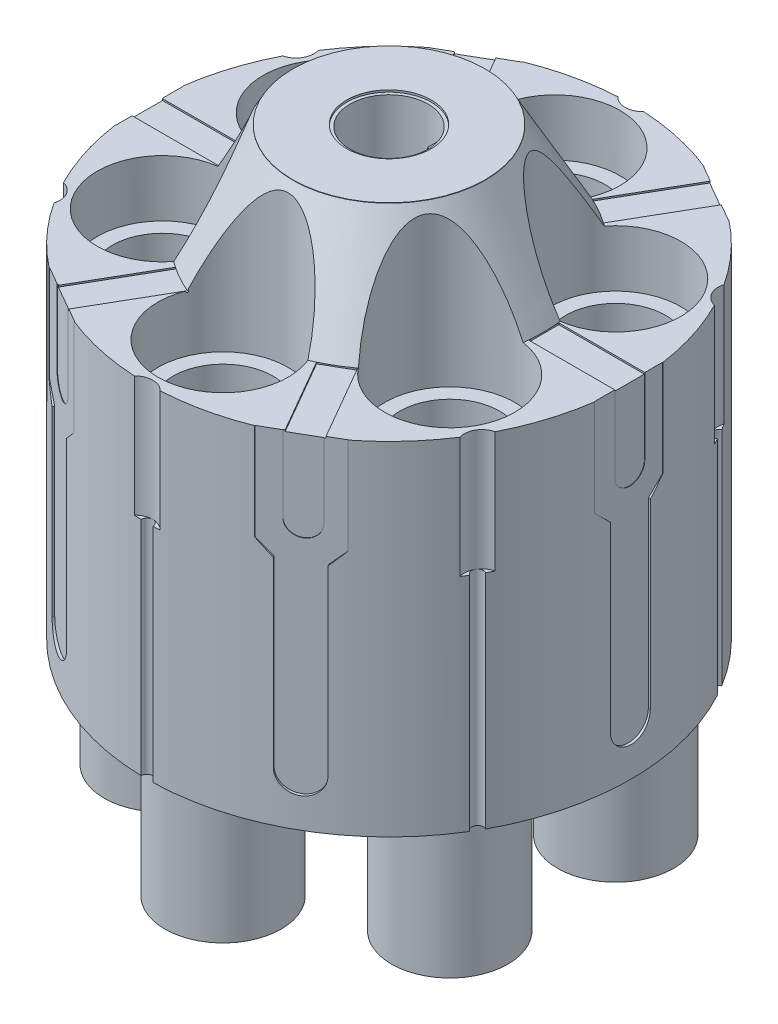
SolidWorks part; units mm, degrees
ref_plane "Front Plane" through (0, 0, 0) normal (0, 0, 1) x (1, 0, 0)
ref_plane "Top Plane" through (0, 0, 0) normal (0, 1, 0) x (1, 0, 0)
ref_plane "Right Plane" through (0, 0, 0) normal (1, 0, 0) x (0, 0, -1)
sketch "Sketch2" plane through (0, 0, 0) normal (0, 1, 0) x (1, 0, 0)
  circle A0 centre (0, 0) radius 30.63
  dimension "D1" = 61.26
extrude "Boss-Extrude2" add sketch "Sketch2" along normal blind 43.34
sketch "Sketch6" plane through (0, 43.34, 0) normal (0, 1, 0) x (1, 0, 0)
  circle A0 centre (0, 0) radius 19.45
  dimension "D1" = 38.9
extrude "Boss-Extrude6" add sketch "Sketch6" along normal blind 13.09
sketch "Sketch8" plane through (0, 0, 0) normal (1, 0, 0) x (0, 0, -1)
  line L0 (0, 56.3789) -> (12.16, 56.3789) construction
  line L1 (0, 31.0365) -> (0, -31.0365) construction
  line L2 (12.16, 56.3789) -> (19.45, 43.34) construction
  line L3 (19.45, 43.34) -> (0, 43.34) construction
  line L4 (30.63, 43.34) -> (-30.63, 43.34) construction
  line L5 (0, 43.34) -> (0, 56.3789) construction
  line L6 (19.45, 43.34) -> (19.45, 56.43)
  line L8 (12.16, 56.3789) -> (19.45, 43.34)
  line L9 (12.16, 56.3789) -> (12.16, 57.4904)
  line L10 (12.16, 57.4904) -> (19.45, 57.4904)
  line L11 (19.45, 57.4904) -> (19.45, 56.43)
  dimension "D1" = 12.16
  dimension "D2" = 13.0389
revolve "Cut-Revolve5" cut sketch "Sketch8" angle 360 about L5
sketch "Sketch9" plane through (0, 56.43, 0) normal (0, 1, 0) x (1, 0, 0)
  line L0 (0, -31.6197) -> (0, 31.6197) construction
  circle A0 centre (0, 20.9948) radius 8.2392
  circle A1 centre (18.182, 10.4974) radius 8.2392
  circle A2 centre (18.182, -10.4974) radius 8.2392
  circle A3 centre (0, -20.9948) radius 8.2392
  circle A4 centre (-18.182, -10.4974) radius 8.2392
  circle A5 centre (-18.182, 10.4974) radius 8.2392
  point P16 (0, 0)
  dimension "D1" = 6
extrude "Cut-Extrude1" cut sketch "Sketch9" against normal blind 20.25
sketch "Sketch10" plane through (0, 36.18, 0) normal (0, 1, 0) x (1, 0, 0)
  line L0 (0, -31.0365) -> (0, 31.0365) construction
  circle A0 centre (0, 20.9948) radius 6.33
  circle A1 centre (0, 20.9948) radius 8.2392 construction
  circle A2 centre (18.182, 10.4974) radius 6.33
  circle A3 centre (18.182, -10.4974) radius 6.33
  circle A4 centre (0, -20.9948) radius 6.33
  circle A5 centre (-18.182, -10.4974) radius 6.33
  circle A6 centre (-18.182, 10.4974) radius 6.33
  point P18 (0, 0)
  dimension "D1" = 12.66
  dimension "D2" = 6
extrude "Cut-Extrude2" cut sketch "Sketch10" against normal through all
sketch "Sketch11" plane through (0, 56.43, 0) normal (0, 1, 0) x (1, 0, 0)
  circle A0 centre (0, 0) radius 4.945
  dimension "D1" = 9.89
extrude "Cut-Extrude3" cut sketch "Sketch11" against normal blind 35.4
sketch "Sketch12" plane through (0, 21.03, 0) normal (0, 1, 0) x (1, 0, 0)
  circle A0 centre (0, 0) radius 2.065
  dimension "D1" = 4.13
extrude "Cut-Extrude4" cut sketch "Sketch12" against normal through all
sketch "Sketch13" plane through (0, 56.43, 0) normal (0, 1, 0) x (1, 0, 0)
  circle A0 centre (0, 0) radius 5.3471
extrude "Cut-Extrude5" cut sketch "Sketch13" against normal blind 0.25
sketch "Sketch15" plane through (0, 21.03, 0) normal (0, 1, 0) x (1, 0, 0)
  line L0 (4.0682, -2.8112) -> (4.0682, -0.81)
  line L1 (4.0682, -0.81) -> (4.8782, -0.81)
  line L2 (4.0682, 2.8112) -> (4.0682, 0.81)
  line L3 (4.0682, 0.81) -> (4.8782, 0.81)
  line L4 (-31.0365, 0) -> (31.0365, 0) construction
  circle A0 centre (0, 0) radius 4.945 construction
  arc A1 (4.0682, -2.8112) -> (4.8782, -0.81) centre (0, 0) ccw
  arc A2 (4.0682, 2.8112) -> (4.8782, 0.81) centre (0, 0) cw
  dimension "D1" = 0.81
  dimension "D2" = 0.81
  dimension "D3" = 0.81
extrude "Boss-Extrude7" add sketch "Sketch15" along normal blind 34.5
sketch "Sketch16" plane through (0, 0, 0) normal (0, -1, 0) x (1, 0, 0)
  circle A0 centre (0, 0) radius 29.6015
  circle A3 centre (-18.182, 10.4974) radius 7.36
  circle A4 centre (0, 20.9948) radius 7.36
  circle A5 centre (18.182, 10.4974) radius 7.36
  circle A6 centre (18.182, -10.4974) radius 7.36
  circle A7 centre (0, -20.9948) radius 7.36
  circle A8 centre (-18.182, -10.4974) radius 7.36
  circle A9 centre (0, 0) radius 4.955
  point P19 (0, 0)
  dimension "D1" = 59.2031
  dimension "D2" = 14.72
  dimension "D4" = 9.91
  dimension "D3" = 6
extrude "Cut-Extrude9" cut sketch "Sketch16" against normal blind 34.5
sketch "Sketch17" plane through (0, 0, 0) normal (0, 1, 0) x (1, 0, 0)
  circle A2 centre (0, 0) radius 4.955
  dimension "D2" = 9.91
extrude "Cut-Extrude12" cut sketch "Sketch17" along normal blind 14.38
sketch "Sketch21" plane through (0, 14.38, 0) normal (0, -1, 0) x (1, 0, 0)
  circle A1 centre (0, 0) radius 3.15
  circle A2 centre (0, 0) radius 4.955
  dimension "D1" = 6.3
extrude "Cut-Extrude14" cut sketch "Sketch21" against normal blind 6.04
sketch "Sketch22" plane through (0, 43.34, 0) normal (0, 1, 0) x (1, 0, 0)
  line L0 (7.9386, 17.6463) -> (16.0129, 31.6314)
  line L1 (11.2272, 15.7476) -> (19.2687, 29.6759)
  line L2 (16.0129, 31.6314) -> (19.2687, 29.6759)
  line L3 (7.9386, 17.6463) -> (11.2272, 15.7476)
  line L4 (19.409, 2.0794) -> (19.409, -1.7179)
  line L5 (19.409, -1.7179) -> (35.492, -1.7179)
  line L6 (35.5576, 2.0794) -> (35.492, -1.7179)
  line L7 (19.409, 2.0794) -> (35.5576, 2.0794)
  line L8 (11.6629, -15.6376) -> (8.3743, -17.5363)
  line L9 (8.3743, -17.5363) -> (16.4158, -31.4646)
  line L10 (19.7372, -29.6227) -> (16.4158, -31.4646)
  line L11 (11.6629, -15.6376) -> (19.7372, -29.6227)
  line L12 (-7.5536, -17.7878) -> (-10.8422, -15.8891)
  line L13 (-10.8422, -15.8891) -> (-18.8837, -29.8174)
  line L14 (-15.6279, -31.7729) -> (-18.8837, -29.8174)
  line L15 (-7.5536, -17.7878) -> (-15.6279, -31.7729)
  line L16 (-19.0239, -2.221) -> (-19.0239, 1.5764)
  line L17 (-19.0239, 1.5764) -> (-35.1069, 1.5764)
  line L18 (-35.1725, -2.221) -> (-35.1069, 1.5764)
  line L19 (-19.0239, -2.221) -> (-35.1725, -2.221)
  line L20 (-11.2778, 15.4961) -> (-7.9892, 17.3947)
  line L21 (-7.9892, 17.3947) -> (-16.0307, 31.3231)
  line L22 (-19.3521, 29.4812) -> (-16.0307, 31.3231)
  line L23 (-11.2778, 15.4961) -> (-19.3521, 29.4812)
  line L25 (-31.0365, 0) -> (31.0365, 0) construction
  point P29 (0.1925, -0.0708)
  dimension "D1" = 6
extrude "Cut-Extrude15" cut sketch "Sketch22" against normal blind 0.2
sketch "Sketch24" plane through (0, 43.34, 0) normal (0, 1, 0) x (1, 0, 0)
  line L0 (30.23, 2.0794) -> (30.23, -1.7179)
  line L1 (30.5593, 2.0794) -> (19.409, 2.0794) construction
  line L2 (19.409, -1.7179) -> (30.5818, -1.7179) construction
  line L3 (30.23, -1.7179) -> (31.9275, -1.7179)
  line L4 (31.9275, -1.7179) -> (31.9275, 2.0794)
  line L5 (31.9275, 2.0794) -> (30.23, 2.0794)
  line L6 (30.63, 0) -> (30.63, 6.5924) construction
  line L7 (-31.0365, 0) -> (31.0365, 0) construction
  line L8 (17.7646, -26.6103) -> (16.9159, -25.1402)
  line L9 (16.9159, -25.1402) -> (13.6272, -27.0389)
  line L10 (13.6272, -27.0389) -> (14.476, -28.509)
  line L11 (14.476, -28.509) -> (17.7646, -26.6103)
  line L12 (-14.1629, -28.6897) -> (-13.3141, -27.2197)
  line L13 (-13.3141, -27.2197) -> (-16.6028, -25.321)
  line L14 (-16.6028, -25.321) -> (-17.4515, -26.791)
  line L15 (-17.4515, -26.791) -> (-14.1629, -28.6897)
  line L16 (-31.9275, -2.0794) -> (-30.23, -2.0794)
  line L17 (-30.23, -2.0794) -> (-30.23, 1.7179)
  line L18 (-30.23, 1.7179) -> (-31.9275, 1.7179)
  line L19 (-31.9275, 1.7179) -> (-31.9275, -2.0794)
  line L20 (-17.7646, 26.6103) -> (-16.9159, 25.1402)
  line L21 (-16.9159, 25.1402) -> (-13.6272, 27.0389)
  line L22 (-13.6272, 27.0389) -> (-14.476, 28.509)
  line L23 (-14.476, 28.509) -> (-17.7646, 26.6103)
  line L24 (14.1629, 28.6897) -> (13.3141, 27.2197)
  line L25 (13.3141, 27.2197) -> (16.6028, 25.321)
  line L26 (16.6028, 25.321) -> (17.4515, 26.791)
  line L27 (17.4515, 26.791) -> (14.1629, 28.6897)
  arc A0 (30.5593, 2.0794) -> (16.8886, 25.5533) centre (0, 0) ccw construction
  point P37 (0, 0)
  dimension "D1" = 0.4
  dimension "D2" = 6
extrude "Cut-Extrude17" cut sketch "Sketch24" against normal blind 9.6
ref_plane "Plane2" through (30.63, 0, 0) normal (1, 0, 0) x (0, 0, -1)
sketch "Sketch26" plane through (30.63, 0, 0) normal (1, 0, 0) x (0, 0, -1)
  line L0 (2.0794, 33.74) -> (-1.7179, 33.74) construction
  line L1 (2.0794, 33.74) -> (-1.7179, 33.74) construction
  line L2 (-1.7179, 33.74) -> (2.0794, 33.74)
  arc A0 (-1.7179, 33.74) -> (2.0794, 33.74) centre (0.1808, 33.74) ccw
extrude "Cut-Extrude18" cut sketch "Sketch26" against normal blind 0.4
pattern_circular "CirPattern1" count 6 over 360 about axis through (0, 43.34, 0) along (0, 1, 0) of "Cut-Extrude18"
sketch "Sketch28" plane through (30.63, 0, 0) normal (1, 0, 0) x (0, 0, -1)
  line L0 (-4.315, 44.0536) -> (4.315, 44.0536)
  line L3 (0, 31.0365) -> (0, -31.0365) construction
  line L4 (-4.315, 44.0536) -> (-4.315, 31.1427)
  line L5 (-4.315, 31.1427) -> (-2.5286, 29.3563)
  line L6 (-2.5286, 29.3563) -> (-2.5286, 6.3189)
  line L7 (4.315, 44.0536) -> (4.315, 31.1427)
  line L8 (4.315, 31.1427) -> (2.5286, 29.3563)
  line L9 (2.5286, 29.3563) -> (2.5286, 6.3189)
  arc A0 (-2.5286, 6.3189) -> (2.5286, 6.3189) centre (0, 6.3189) ccw
  dimension "D1" = 4.315
  dimension "D2" = 4.315
extrude "Cut-Extrude19" cut sketch "Sketch28" against normal blind 0.35
pattern_circular "CirPattern2" count 6 over 360 about axis through (0, 0, 0) along (0, 1, 0) of "Cut-Extrude19"
sketch "Sketch29" plane through (0, 43.34, 0) normal (0, 1, 0) x (1, 0, 0)
  line L0 (-0.7499, 30.6208) -> (-0.7499, 31.6611)
  line L1 (-0.7499, 31.6611) -> (0.7499, 31.6611)
  line L2 (0.7499, 31.6611) -> (0.7499, 30.6208)
  arc A1 (11.4254, 28.4193) -> (-11.4254, 28.4193) centre (0, 0) ccw construction
  arc A2 (-0.7499, 30.6208) -> (0.7499, 30.6208) centre (0, 30.63) ccw
  dimension "D1" = 0.75
extrude "Cut-Extrude23" cut sketch "Sketch29" against normal through all
sketch "Sketch30" plane through (0, 0, 0) normal (0, 1, 0) x (1, 0, 0)
  line L0 (0, -31.0365) -> (0, 31.0365) construction
  line L1 (-1.6376, 30.5862) -> (-1.6376, 31.7494)
  line L2 (-1.6376, 31.7494) -> (1.6376, 31.7494)
  line L3 (1.6376, 31.7494) -> (1.6376, 30.5862)
  arc A0 (-1.6376, 30.5862) -> (1.6376, 30.5862) centre (0, 32.1317) ccw
  arc A1 (-0.7499, 30.6208) -> (-11.4254, 28.4193) centre (0, 0) ccw construction
  arc A2 (11.4254, 28.4193) -> (0.7499, 30.6208) centre (0, 0) ccw construction
  arc A3 (-0.7499, 30.6208) -> (0.7499, 30.6208) centre (0, 30.63) ccw construction
extrude "Cut-Extrude24" cut sketch "Sketch30" against normal blind 15.26 from surface at 43.34 starting at face at (1.8804, 43.34, -26.1665)
pattern_circular "CirPattern3" count 6 over 360 about axis through (0, 0, 0) along (0, 1, 0) of "Cut-Extrude24"
pattern_circular "CirPattern4" count 6 over 360 about axis through (0, 0, 0) along (0, 1, 0) of "Cut-Extrude23"
sketch "Sketch31" plane through (0, 0, 0) normal (0, 1, 0) x (1, 0, 0)
  circle A0 centre (0, -20.9948) radius 6.33
  circle A1 centre (0, -20.9948) radius 7.36
  circle A2 centre (-18.182, -10.4974) radius 7.36
  circle A3 centre (-18.182, 10.4974) radius 7.36
  circle A4 centre (0, 20.9948) radius 7.36
  circle A5 centre (18.182, 10.4974) radius 7.36
  circle A6 centre (18.182, -10.4974) radius 7.36
  circle A7 centre (-18.182, -10.4974) radius 6.33
  circle A8 centre (-18.182, 10.4974) radius 6.33
  circle A9 centre (0, 20.9948) radius 6.33
  circle A10 centre (18.182, 10.4974) radius 6.33
  circle A11 centre (18.182, -10.4974) radius 6.33
  point P16 (0, 0)
  point P27 (0, 0)
  dimension "D1" = 6
  dimension "D2" = 6
extrude "Boss-Extrude10" add sketch "Sketch31" against normal blind 17.57
